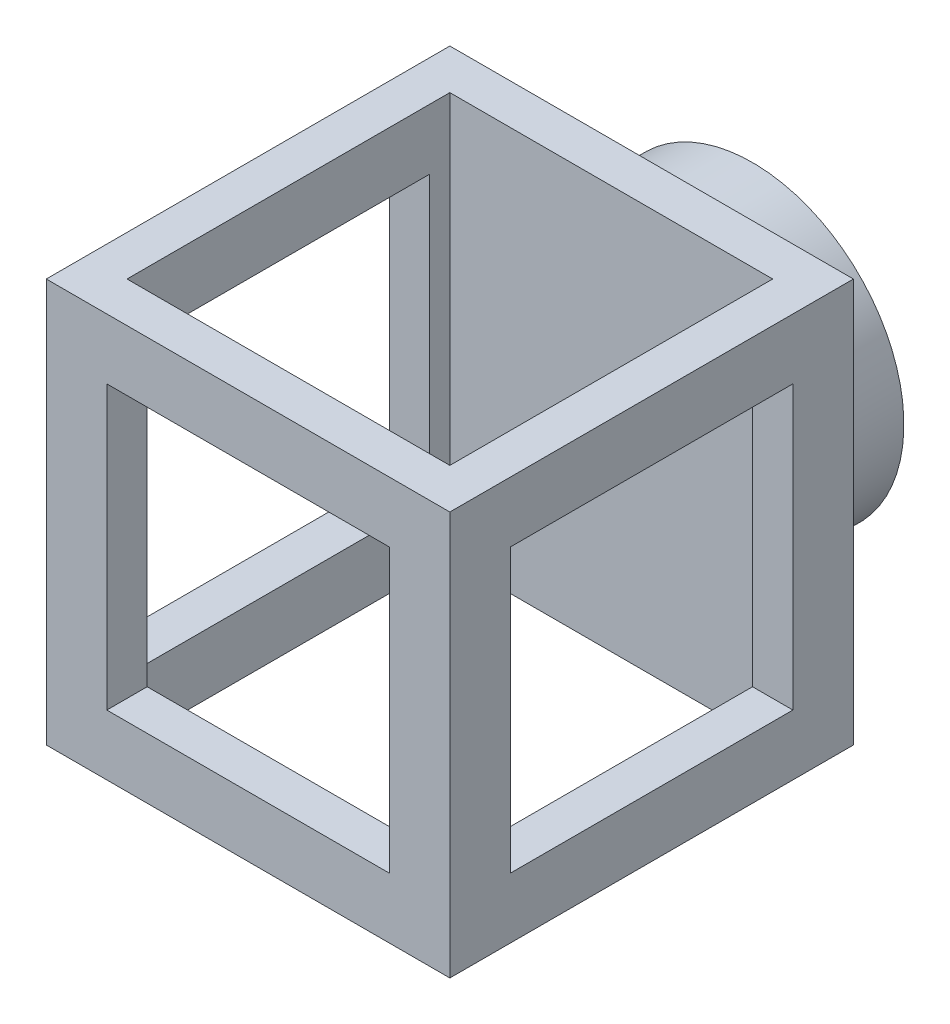
SolidWorks part; units mm, degrees
ref_plane "Front Plane" through (0, 0, 0) normal (0, 0, 1) x (1, 0, 0)
ref_plane "Top Plane" through (0, 0, 0) normal (0, 1, 0) x (1, 0, 0)
ref_plane "Right Plane" through (0, 0, 0) normal (1, 0, 0) x (0, 0, -1)
sketch "Sketch1" plane through (0, 0, 0) normal (0, 1, 0) x (1, 0, 0)
  line L0 (-8, 8) -> (8, 8)
  line L1 (-10, 10) -> (10, 10)
  line L2 (-10, 10) -> (-10, -10)
  line L3 (-10, -10) -> (10, -10)
  line L4 (10, 10) -> (10, -10)
  line L5 (-10, 10) -> (10, -10) construction
  line L6 (-10, -10) -> (10, 10) construction
  line L7 (8, 8) -> (8, -8)
  line L8 (-8, -8) -> (8, -8)
  line L9 (-8, 8) -> (-8, -8)
  point P0 (0, 0)
  dimension "D1" = 20
  dimension "D2" = 20
  dimension "D3" = 2
extrude "Boss-Extrude1" add sketch "Sketch1" along normal mid plane 20
sketch "Sketch2" plane through (0, 0, 10) normal (0, 0, 1) x (1, 0, 0)
  line L14 (-7, -7) -> (7, -7)
  line L15 (7, -7) -> (7, 7)
  line L16 (-7, 7) -> (-7, -7)
  line L17 (7, 7) -> (-7, 7)
  line L18 (-7, -7) -> (7, -7)
  line L19 (7, -7) -> (7, 7)
  line L20 (-7, 7) -> (-7, -7)
  line L21 (7, 7) -> (-7, 7)
  dimension "D1" = 3
extrude "Cut-Extrude1" cut sketch "Sketch2" against normal through all
sketch "Sketch3" plane through (10, 0, 0) normal (1, 0, 0) x (0, 0, -1)
  line L8 (-7, -7) -> (7, -7)
  line L9 (7, -7) -> (7, 7)
  line L10 (7, 7) -> (-7, 7)
  line L11 (-7, 7) -> (-7, -7)
  line L12 (-7, -7) -> (7, -7)
  line L13 (7, -7) -> (7, 7)
  line L14 (7, 7) -> (-7, 7)
  line L15 (-7, 7) -> (-7, -7)
  dimension "D1" = 3
extrude "Cut-Extrude2" cut sketch "Sketch3" against normal through all
sketch "Sketch4" plane through (-7, 0, 0) normal (1, 0, 0) x (0, 0, -1)
  line L4 (8, 7) -> (8, -7)
  line L5 (8, -7) -> (10, -7)
  line L6 (10, -7) -> (10, 7)
  line L7 (10, 7) -> (8, 7)
  line L8 (8, 7) -> (8, -7)
  line L9 (8, -7) -> (10, -7)
  line L10 (10, -7) -> (10, 7)
  line L11 (10, 7) -> (8, 7)
  dimension "D1" = 0
extrude "Boss-Extrude2" add sketch "Sketch4" along normal up to surface (14 mm away) up to face at (7, 0, -9)
sketch "Sketch5" plane through (0, 0, -10) normal (0, 0, -1) x (-1, 0, 0)
  circle A0 centre (0, 0) radius 7.5
  dimension "D1" = 15
extrude "Boss-Extrude3" add sketch "Sketch5" along normal blind 5
